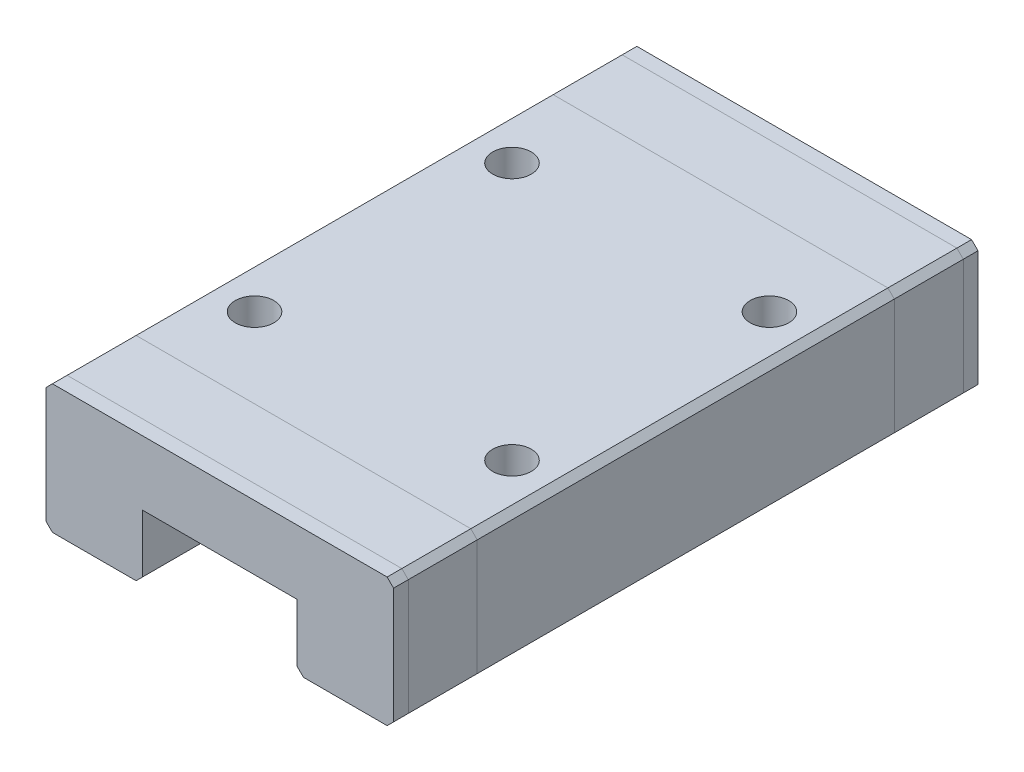
SolidWorks part; units mm, degrees
ref_plane "前视基准面" through (0, 0, 0) normal (0, 0, 1) x (1, 0, 0)
ref_plane "上视基准面" through (0, 0, 0) normal (0, 1, 0) x (1, 0, 0)
ref_plane "右视基准面" through (0, 0, 0) normal (1, 0, 0) x (0, 0, -1)
sketch "草图1" plane through (0, 0, 0) normal (0, 0, 1) x (1, 0, 0)
  line L0 (13.5, 10) -> (13.5, 3.5) construction
  line L1 (0, 0) -> (7.5, 0)
  line L2 (0, 0) -> (0, 10)
  line L3 (0, 10) -> (27, 10)
  line L4 (27, 0) -> (27, 10)
  line L5 (19.5, 0) -> (27, 0)
  line L7 (7.5, 0) -> (7.5, 5)
  line L8 (7.5, 5) -> (19.5, 5)
  line L9 (19.5, 0) -> (19.5, 5)
  dimension "D1" = 27
  dimension "D2" = 10
  dimension "D3" = 12
  dimension "D4" = 5
extrude "凸台-拉伸1" add sketch "草图1" along normal blind 45.4
sketch "草图2" plane through (0, 10, 0) normal (0, 1, 0) x (1, 0, 0)
  line L0 (27, -22.7) -> (0, -22.7) construction
  line L1 (27, -45.4) -> (27, 0) construction
  line L2 (0, -45.4) -> (0, 0) construction
  line L3 (13.5, 0) -> (13.5, -45.4) construction
  line L4 (27, 0) -> (0, 0) construction
  line L5 (27, -45.4) -> (0, -45.4) construction
  line L7 (23.5, -12.7) -> (3.5, -12.7) construction
  line L8 (23.5, -12.7) -> (23.5, -32.7) construction
  line L9 (23.5, -32.7) -> (3.5, -32.7) construction
  line L10 (3.5, -12.7) -> (3.5, -32.7) construction
  line L11 (23.5, -12.7) -> (3.5, -32.7) construction
  line L12 (23.5, -32.7) -> (3.5, -12.7) construction
  circle A0 centre (23.5, -12.7) radius 1.5
  circle A1 centre (3.5, -12.7) radius 1.5
  circle A2 centre (23.5, -32.7) radius 1.5
  circle A3 centre (3.5, -32.7) radius 1.5
  point P12 (13.5, -22.7)
  dimension "D1" = 3
  dimension "D2" = 20
  dimension "D3" = 20
extrude "切除-拉伸1" cut sketch "草图2" against normal blind 2.5
chamfer "倒角1" distance 0.5 angle 45 6 edges at (19.5, 0, 22.7) (7.5, 0, 22.7) (27, 0, 22.7) (0, 0, 22.7) (27, 10, 22.7) (0, 10, 22.7)
sketch "草图3" plane through (0, 10, 0) normal (0, 1, 0) x (1, 0, 0)
  line L0 (26.5, -22.7) -> (0.5, -22.7) construction
  line L1 (26.5, -45.4) -> (26.5, 0) construction
  line L2 (0.5, 0) -> (0.5, -45.4) construction
  line L3 (26.5, -44.2594) -> (0.5, -44.2594)
  line L4 (26.5, -38.9) -> (0.5, -38.9)
  line L5 (26.5, -38.9) -> (26.5, -45.4)
  line L6 (26.5, -45.4) -> (0.5, -45.4)
  line L7 (0.5, -38.9) -> (0.5, -45.4)
  line L8 (0.5, -6.5) -> (0.5, 0)
  line L9 (26.5, 0) -> (0.5, 0)
  line L10 (26.5, -6.5) -> (26.5, 0)
  line L11 (26.5, -6.5) -> (0.5, -6.5)
  line L12 (26.5, -1.1406) -> (0.5, -1.1406)
  dimension "D1" = 1.1406
  dimension "D2" = 32.4
split line "分割线1"
sketch "草图4" plane through (0, 0, 0) normal (-1, 0, 0) x (0, 0, 1)
  line L0 (45.4, 0) -> (0, 0) construction
  line L1 (0, 10) -> (6.5, 10)
  line L2 (0, 10) -> (0, 0)
  line L3 (0, 0) -> (6.5, 0)
  line L4 (6.5, 10) -> (6.5, 0)
  line L5 (1.1406, 10) -> (1.1406, 0)
  line L6 (22.7, 9.5) -> (22.7, 0.5) construction
  line L7 (45.4, 9.5) -> (0, 9.5) construction
  line L8 (0, 0.5) -> (45.4, 0.5) construction
  line L9 (44.2594, 10) -> (44.2594, 0)
  line L10 (38.9, 10) -> (38.9, 0)
  line L11 (45.4, 0) -> (38.9, 0)
  line L12 (45.4, 10) -> (45.4, 0)
  line L13 (45.4, 10) -> (38.9, 10)
split line "分割线2"
sketch "草图5" plane through (0, 0, 0) normal (0, -1, 0) x (1, 0, 0)
  line L0 (26.5, 44.2594) -> (0.5, 44.2594) construction
  line L1 (26.5, 1.1406) -> (0.5, 1.1406) construction
  line L2 (26.5, 44.2594) -> (0.5, 44.2594)
  line L3 (26.5, 1.1406) -> (0.5, 1.1406)
  line L4 (0.5, 38.9) -> (26.5, 38.9)
  line L5 (0.5, 45.4) -> (0.5, 38.9)
  line L6 (26.5, 45.4) -> (0.5, 45.4)
  line L7 (26.5, 38.9) -> (26.5, 45.4)
  line L8 (0.5, 38.9) -> (26.5, 38.9)
  line L9 (0.5, 45.4) -> (0.5, 38.9)
  line L10 (26.5, 45.4) -> (0.5, 45.4)
  line L11 (26.5, 38.9) -> (26.5, 45.4)
  line L12 (26.5, 0) -> (26.5, 6.5)
  line L13 (26.5, 6.5) -> (0.5, 6.5)
  line L14 (0.5, 6.5) -> (0.5, 0)
  line L15 (0.5, 0) -> (26.5, 0)
  line L16 (26.5, 0) -> (26.5, 6.5)
  line L17 (26.5, 6.5) -> (0.5, 6.5)
  line L18 (0.5, 6.5) -> (0.5, 0)
  line L19 (0.5, 0) -> (26.5, 0)
  dimension "D1" = 0
  dimension "D2" = 0
split line "分割线3"
